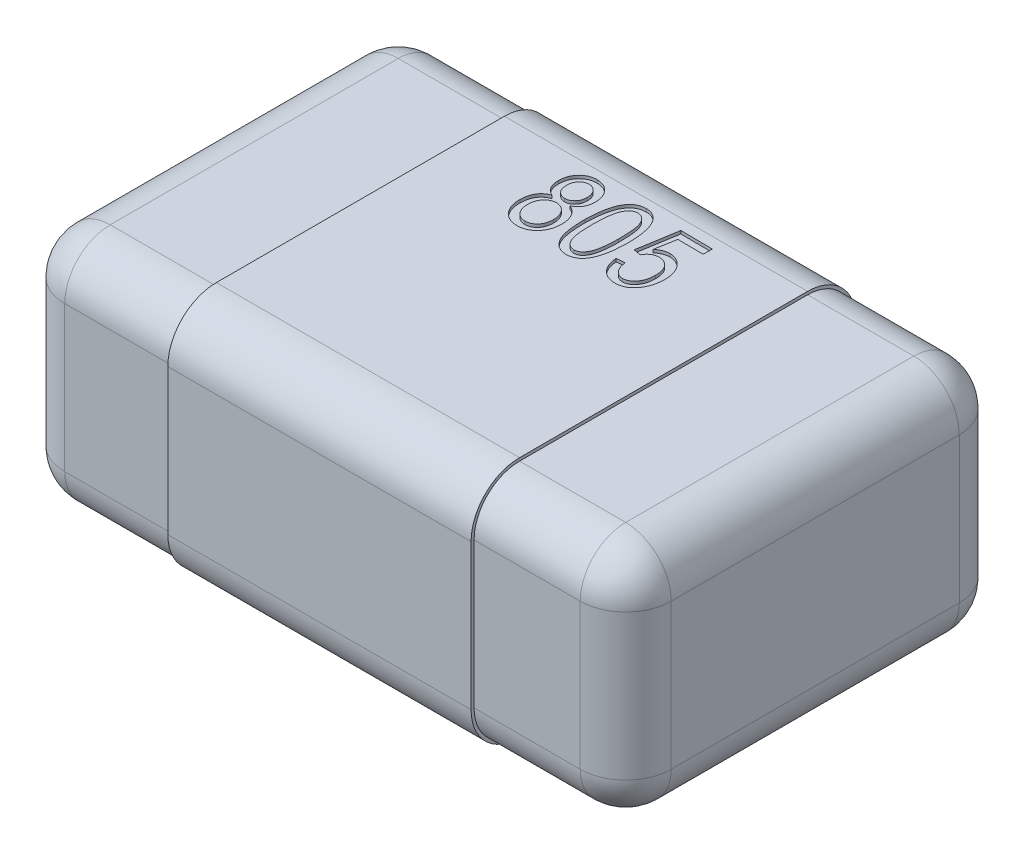
SolidWorks part; units mm, degrees
material "Aço inoxidável fundido"
ref_plane "Plano frontal" through (0, 0, 0) normal (0, 0, 1) x (1, 0, 0)
ref_plane "Plano superior" through (0, 0, 0) normal (0, 1, 0) x (1, 0, 0)
ref_plane "Plano direito" through (0, 0, 0) normal (1, 0, 0) x (0, 0, -1)
ref_plane "Plano1" through (0, 0.78, 0) normal (0, 1, 0) x (1, 0, 0)
sketch "Esboço1" plane through (0, 0.78, 0) normal (0, 1, 0) x (1, 0, 0)
  line L0 (-1, -0.625) -> (1, -0.625)
  line L1 (1, -0.625) -> (1, 0.625)
  line L2 (1, 0.625) -> (-1, 0.625)
  line L3 (-1, 0.625) -> (-1, -0.625)
extrude "Ressalto-extrusão1" add sketch "Esboço1" against normal blind 0.78
ref_plane "Plano2" through (0, 0.882, 0) normal (0, -1, 0) x (0, 0, 1)
fillet "Filete1" radius 0.15 12 edges at (0, 0, -0.625) (-1, 0.39, -0.625) (1, 0.39, -0.625) (0, 0.78, -0.625) (-1, 0, 0) (1, 0, 0) (0, 0, 0.625) (-1, 0.78, 0) (1, 0.78, 0) (-1, 0.39, 0.625) (1, 0.39, 0.625) (0, 0.78, 0.625)
sketch "Esboço4" plane through (0, 0, 0) normal (1, 0, 0) x (0, 0, -1)
  line L0 (0.625, 0.15) -> (0.625, 0.63) construction
  line L1 (0.625, 0.15) -> (0.625, 0.63)
  line L2 (0.475, 0) -> (-0.475, 0) construction
  line L3 (0.475, 0) -> (-0.475, 0)
  line L4 (0.475, 0.78) -> (-0.475, 0.78) construction
  line L5 (-0.625, 0.63) -> (-0.625, 0.15) construction
  line L6 (0.475, 0.78) -> (-0.475, 0.78)
  line L7 (-0.625, 0.63) -> (-0.625, 0.15)
  line L8 (0.635, 0.15) -> (0.635, 0.63)
  line L9 (0.475, 0.79) -> (-0.475, 0.79)
  line L10 (-0.635, 0.63) -> (-0.635, 0.15)
  line L11 (0.475, -0.01) -> (-0.475, -0.01)
  arc A5 (0.475, 0) -> (0.625, 0.15) centre (0.475, 0.15) ccw construction
  arc A6 (0.475, 0) -> (0.625, 0.15) centre (0.475, 0.15) ccw
  arc A7 (-0.475, 0.78) -> (-0.625, 0.63) centre (-0.475, 0.63) ccw construction
  arc A8 (-0.625, 0.15) -> (-0.475, 0) centre (-0.475, 0.15) ccw construction
  arc A9 (-0.475, 0.78) -> (-0.625, 0.63) centre (-0.475, 0.63) ccw
  arc A10 (-0.625, 0.15) -> (-0.475, 0) centre (-0.475, 0.15) ccw
  arc A11 (0.625, 0.63) -> (0.475, 0.78) centre (0.475, 0.63) ccw construction
  arc A12 (0.625, 0.63) -> (0.475, 0.78) centre (0.475, 0.63) ccw
  arc A13 (0.635, 0.63) -> (0.475, 0.79) centre (0.475, 0.63) ccw
  arc A14 (-0.475, 0.79) -> (-0.635, 0.63) centre (-0.475, 0.63) ccw
  arc A15 (-0.635, 0.15) -> (-0.475, -0.01) centre (-0.475, 0.15) ccw
  arc A16 (0.475, -0.01) -> (0.635, 0.15) centre (0.475, 0.15) ccw
  dimension "D1" = 0.01
extrude "Ressalto-extrusão4" add sketch "Esboço4" along normal blind 0.5 and the other way blind 0.5
sketch "Esboço2" plane through (0, 0.79, 0) normal (0, -1, 0) x (0, 0, 1)
  line L7 (-0.1842, -0.2414) -> (-0.1885, 0.2586) construction
  text T0 "805" font "Arial Narrow" height in points 1
extrude "Corte-extrusão1" cut sketch "Esboço2" along normal up to surface (0.01 mm away) up to face at (-0.675, 0.78, 0)
